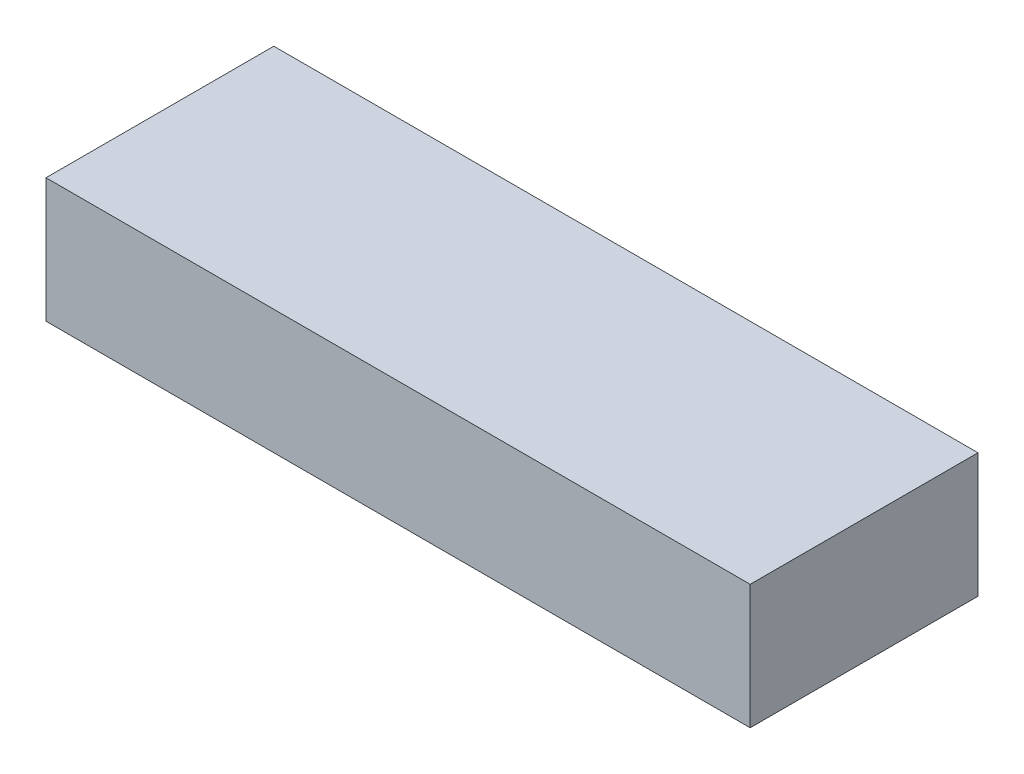
SolidWorks part; units mm, degrees
ref_plane "Front Plane" through (0, 0, 0) normal (0, 0, 1) x (1, 0, 0)
ref_plane "Top Plane" through (0, 0, 0) normal (0, 1, 0) x (1, 0, 0)
ref_plane "Right Plane" through (0, 0, 0) normal (1, 0, 0) x (0, 0, -1)
sketch "Sketch1" plane through (0, 0, 0) normal (0, 1, 0) x (1, 0, 0)
  line L1 (-60.7044, 34.5667) -> (75.2956, 34.5667)
  line L2 (-60.7044, 34.5667) -> (-60.7044, -9.4333)
  line L3 (-60.7044, -9.4333) -> (75.2956, -9.4333)
  line L4 (75.2956, 34.5667) -> (75.2956, -9.4333)
  dimension "D1" = 136
  dimension "D2" = 44
extrude "Boss-Extrude1" add sketch "Sketch1" along normal blind 24
